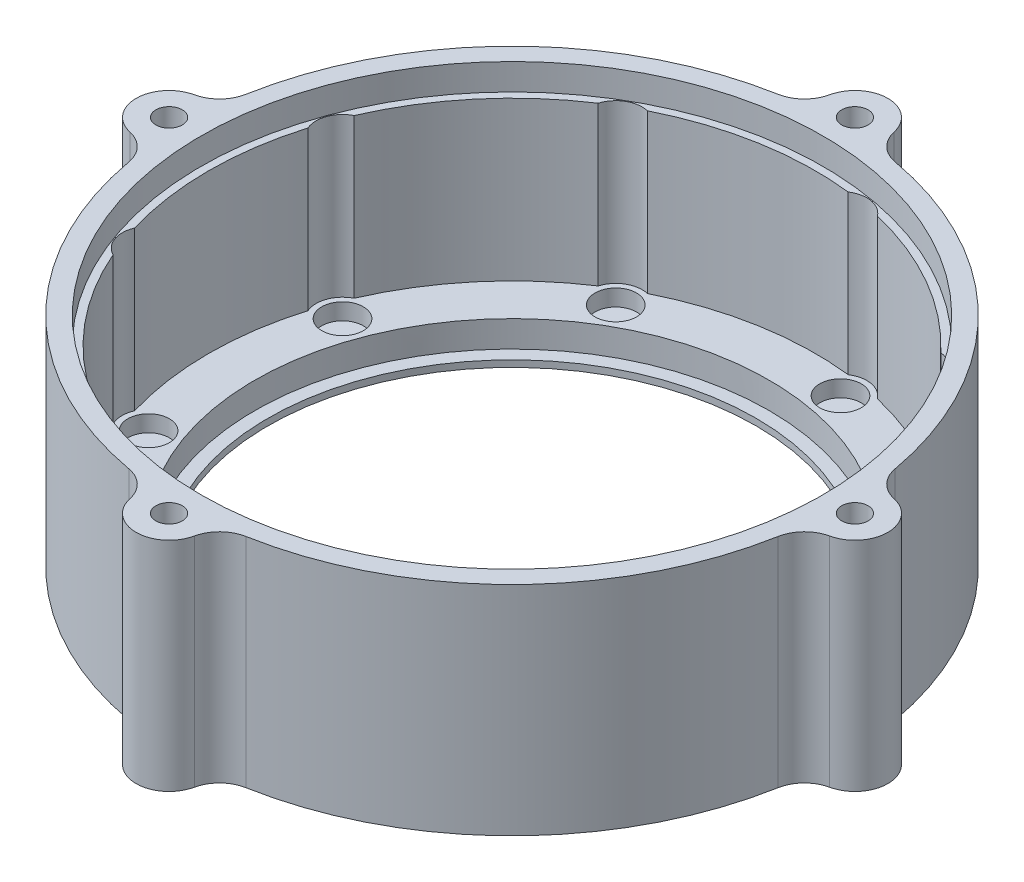
SolidWorks part; units mm, degrees
material "PET"
ref_plane "Front Plane" through (0, 0, 0) normal (0, 0, 1) x (1, 0, 0)
ref_plane "Top Plane" through (0, 0, 0) normal (0, 1, 0) x (1, 0, 0)
ref_plane "Right Plane" through (0, 0, 0) normal (1, 0, 0) x (0, 0, -1)
sketch "Sketch1" plane through (0, 0, 0) normal (0, 1, 0) x (1, 0, 0)
  line L0 (0, 0) -> (50, 0) construction
  circle A0 centre (0, 0) radius 50
  dimension "D1" = 100
extrude "Boss-Extrude1" add sketch "Sketch1" along normal blind 5
sketch "Sketch2" plane through (0, 5, 0) normal (0, 1, 0) x (1, 0, 0)
  line L0 (0, 0) -> (50, 0) construction
  circle A0 centre (0, 0) radius 50 construction
  circle A1 centre (43, 0) radius 3
  circle A2 centre (32.9399, -27.6399) radius 3
  circle A3 centre (7.4669, -42.3467) radius 3
  circle A4 centre (-21.5, -37.2391) radius 3
  circle A5 centre (-40.4068, -14.7069) radius 3
  circle A6 centre (-40.4068, 14.7069) radius 3
  circle A7 centre (-21.5, 37.2391) radius 3
  circle A8 centre (7.4669, 42.3467) radius 3
  circle A9 centre (32.9399, 27.6399) radius 3
  point P30 (0, 0)
  dimension "D1" = 6
  dimension "D2" = 43
  dimension "D3" = 9
extrude "Boss-Extrude2" add sketch "Sketch2" along normal blind 30
sketch "Sketch3" plane through (0, 5, 0) normal (0, 1, 0) x (1, 0, 0)
  circle A45 centre (0, 0) radius 50
  arc A46 (45.9186, 2.7353) -> (36.9339, 27.4206) centre (0, 0) ccw
  arc A50 (45.9186, -2.7353) -> (45.9186, 2.7353) centre (43, 0) ccw
  arc A60 (33.4175, -31.6113) -> (36.9339, -27.4206) centre (32.9399, -27.6399) ccw
  arc A69 (5.28, -45.696) -> (10.6674, -44.746) centre (7.4669, -42.3467) ccw
  arc A70 (-25.3281, -38.399) -> (-20.5905, -41.1343) centre (-21.5, -37.2391) ccw
  arc A71 (-44.0849, -13.1348) -> (-42.2139, -18.2754) centre (-40.4068, -14.7069) ccw
  arc A72 (-42.2139, 18.2754) -> (-44.0849, 13.1348) centre (-40.4068, 14.7069) ccw
  arc A73 (-20.5905, 41.1343) -> (-25.3281, 38.399) centre (-21.5, 37.2391) ccw
  arc A74 (10.6674, 44.746) -> (5.28, 45.696) centre (7.4669, 42.3467) ccw
  arc A75 (36.9339, 27.4206) -> (33.4175, 31.6113) centre (32.9399, 27.6399) ccw
  arc A76 (36.9339, -27.4206) -> (45.9186, -2.7353) centre (0, 0) ccw
  arc A77 (10.6674, -44.746) -> (33.4175, -31.6113) centre (0, 0) ccw
  arc A78 (-20.5905, -41.1343) -> (5.28, -45.696) centre (0, 0) ccw
  arc A79 (-42.2139, -18.2754) -> (-25.3281, -38.399) centre (0, 0) ccw
  arc A80 (-44.0849, 13.1348) -> (-44.0849, -13.1348) centre (0, 0) ccw
  arc A81 (-25.3281, 38.399) -> (-42.2139, 18.2754) centre (0, 0) ccw
  arc A82 (5.28, 45.696) -> (-20.5905, 41.1343) centre (0, 0) ccw
  arc A83 (33.4175, 31.6113) -> (10.6674, 44.746) centre (0, 0) ccw
  point P25 (0, 0)
  dimension "D1" = 100
  dimension "D2" = 4
extrude "Boss-Extrude3" add sketch "Sketch3" along normal blind 28
sketch "Sketch4" plane through (0, 5, 0) normal (0, 1, 0) x (1, 0, 0)
  circle A0 centre (0, 0) radius 39
  dimension "D1" = 78
extrude "Cut-Extrude1" cut sketch "Sketch4" against normal blind 6
sketch "Sketch5" plane through (0, 5, 0) normal (0, 1, 0) x (1, 0, 0)
  circle A0 centre (43, 0) radius 3
  circle A1 centre (32.9399, -27.6399) radius 3
  circle A2 centre (7.4669, -42.3467) radius 3
  circle A3 centre (-21.5, -37.2391) radius 3
  circle A4 centre (-40.4068, -14.7069) radius 3
  circle A5 centre (-40.4068, 14.7069) radius 3
  circle A6 centre (-21.5, 37.2391) radius 3
  circle A7 centre (7.4669, 42.3467) radius 3
  circle A8 centre (32.9399, 27.6399) radius 3
  point P26 (0, 0)
  dimension "D1" = 9
extrude "Cut-Extrude2" cut sketch "Sketch5" along normal mid plane 88
sketch "Sketch6" plane through (0, 0, 0) normal (0, -1, 0) x (1, 0, 0)
  circle A0 centre (0, 0) radius 39
  circle A1 centre (0, 0) radius 50
extrude "Boss-Extrude4" add sketch "Sketch6" against normal blind 3
sketch "Sketch7" plane through (0, 33, 0) normal (0, 1, 0) x (1, 0, 0)
  circle A3 centre (0, 0) radius 46
  circle A4 centre (0, 0) radius 47
  dimension "D1" = 92
  dimension "D2" = 94
extrude "Cut-Extrude3" cut sketch "Sketch7" against normal blind 4
sketch "Sketch8" plane through (0, 0, 0) normal (0, -1, 0) x (1, 0, 0)
  circle A0 centre (0, 0) radius 39
  circle A1 centre (0, 0) radius 37
  dimension "D1" = 2
extrude "Boss-Extrude5" add sketch "Sketch8" against normal blind 1
sketch "Sketch9" plane through (0, 33, 0) normal (0, 1, 0) x (1, 0, 0)
  line L1 (0, 0) -> (0, 52) construction
  line L3 (0, 0) -> (52, 0) construction
  circle A0 centre (52, 0) radius 2
  circle A2 centre (52, 0) radius 5
  circle A3 centre (-52, 0) radius 2
  circle A4 centre (-52, 0) radius 5
  circle A5 centre (0, 52) radius 2
  circle A6 centre (0, 52) radius 5
  circle A7 centre (0, -52) radius 2
  circle A8 centre (0, -52) radius 5
  dimension "D2" = 4
  dimension "D1" = 52
  dimension "D4" = 4
  dimension "D5" = 3
  dimension "D6" = 52
  dimension "D3" = 3
extrude "Boss-Extrude6" add sketch "Sketch9" against normal up to surface (33 mm away) up to face at (0, 0, 50)
fillet "Fillet1" radius 5 8 edges at (4.489, 16.5, -49.7981) (-4.489, 16.5, -49.7981) (49.7981, 16.5, 4.489) (49.7981, 16.5, -4.489) (-4.489, 16.5, 49.7981) (4.489, 16.5, 49.7981) (-49.7981, 16.5, -4.489) (-49.7981, 16.5, 4.489)
sketch "Sketch10" plane through (0, 5, 0) normal (0, 1, 0) x (1, 0, 0)
  circle A1 centre (32.9399, -27.6399) radius 3.15
  circle A2 centre (43, 0) radius 3.15
  circle A3 centre (43, 0) radius 3.15
  circle A4 centre (7.4669, -42.3467) radius 3.15
  circle A5 centre (-21.5, -37.2391) radius 3.15
  circle A6 centre (-40.4068, -14.7069) radius 3.15
  circle A7 centre (-40.4068, 14.7069) radius 3.15
  circle A8 centre (-21.5, 37.2391) radius 3.15
  circle A9 centre (7.4669, 42.3467) radius 3.15
  circle A10 centre (32.9399, 27.6399) radius 3.15
  point P22 (0, 0)
  dimension "D1" = 0.15
  dimension "D2" = 9
extrude "Cut-Extrude6" cut sketch "Sketch10" against normal blind 2.5
sketch "Sketch11" plane through (0, 33, 0) normal (0, 1, 0) x (1, 0, 0)
  circle A2 centre (0, 0) radius 47.15
  circle A4 centre (0, 0) radius 47.15
  dimension "D1" = 0.15
extrude "Cut-Extrude7" cut sketch "Sketch11" against normal blind 4
